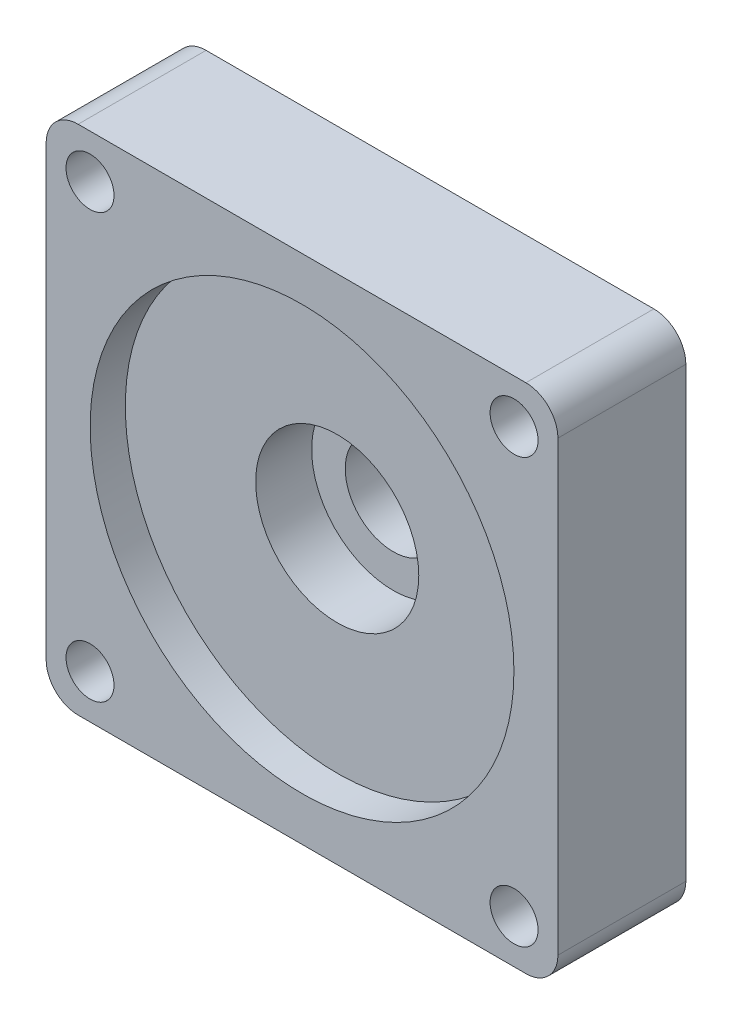
SolidWorks part; units mm, degrees
ref_plane "前视基准面" through (0, 0, 0) normal (0, 0, 1) x (1, 0, 0)
ref_plane "上视基准面" through (0, 0, 0) normal (0, 1, 0) x (1, 0, 0)
ref_plane "右视基准面" through (0, 0, 0) normal (1, 0, 0) x (0, 0, -1)
sketch "草图1" plane through (0, 0, 0) normal (0, 0, 1) x (1, 0, 0)
  line L1 (-16, 16) -> (16, 16)
  line L2 (-16, 16) -> (-16, -16)
  line L3 (-16, -16) -> (16, -16)
  line L4 (16, 16) -> (16, -16)
  line L5 (0, -16) -> (0, 16) construction
  line L6 (-16, 0) -> (16, 0) construction
  point P0 (0, 0)
  dimension "D1" = 32
  dimension "D2" = 32
extrude "凸台-拉伸1" add sketch "草图1" along normal blind 8
sketch "草图2" plane through (0, 0, 8) normal (0, 0, 1) x (1, 0, 0)
  circle A0 centre (-13.2583, 13.2583) radius 1.5
  circle A1 centre (13.2583, 13.2583) radius 1.5
  circle A2 centre (13.2583, -13.2583) radius 1.5
  circle A3 centre (-13.2583, -13.2583) radius 1.5
  point P11 (0, 0)
  dimension "D2" = 3
  dimension "D3" = 37.5
  dimension "D1" = 4
extrude "切除-拉伸1" cut sketch "草图2" against normal up to next
sketch "草图3" plane through (0, 0, 8) normal (0, 0, 1) x (1, 0, 0)
  circle A0 centre (0, 0) radius 13.25
  dimension "D1" = 26.5
extrude "切除-拉伸2" cut sketch "草图3" against normal blind 2.2
sketch "草图4" plane through (0, 0, 5.8) normal (0, 0, 1) x (1, 0, 0)
  circle A0 centre (0, 0) radius 5.1
  dimension "D1" = 10.2
extrude "切除-拉伸3" cut sketch "草图4" against normal blind 3.5
sketch "草图5" plane through (0, 0, 2.3) normal (0, 0, 1) x (1, 0, 0)
  circle A0 centre (0, 0) radius 3
  dimension "D1" = 6
extrude "切除-拉伸4" cut sketch "草图5" against normal up to next
fillet "圆角1" radius 2 4 edges at (-16, -16, 4) (-16, 16, 4) (16, 16, 4) (16, -16, 4)
